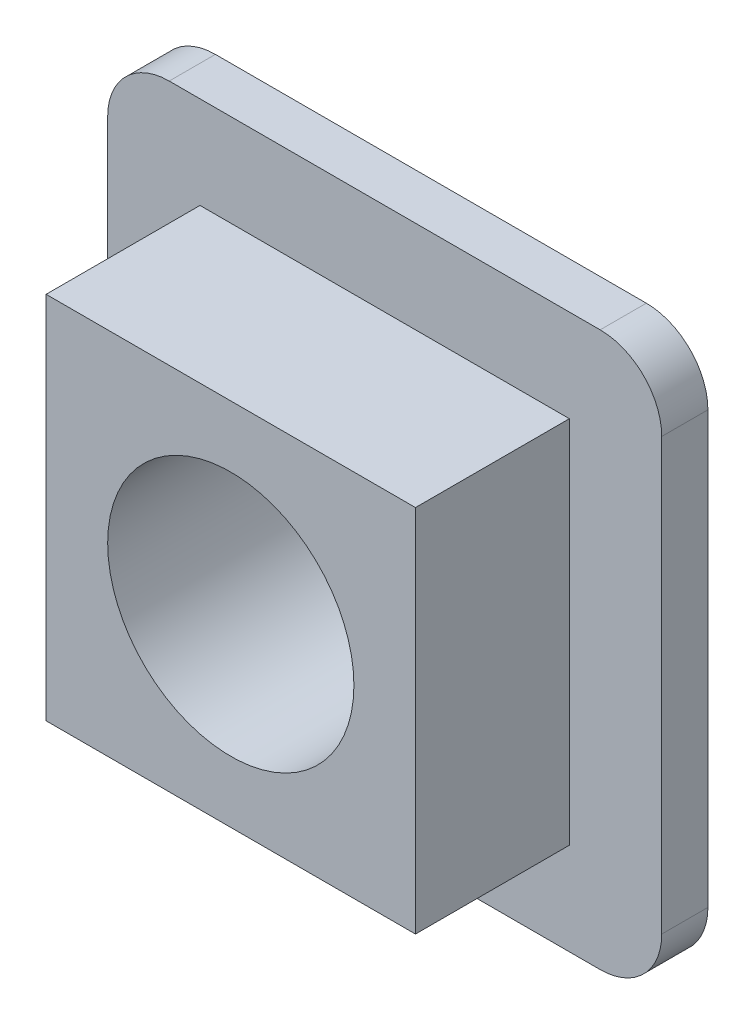
SolidWorks part; units mm, degrees
material "AISI 304"
ref_plane "Front Plane" through (0, 0, 0) normal (0, 0, 1) x (1, 0, 0)
ref_plane "Top Plane" through (0, 0, 0) normal (0, 1, 0) x (1, 0, 0)
ref_plane "Right Plane" through (0, 0, 0) normal (1, 0, 0) x (0, 0, -1)
sketch "Sketch1" plane through (0, 0, 0) normal (0, 0, 1) x (1, 0, 0)
  line L1 (2, 0) -> (16, 0)
  line L2 (0, 2) -> (0, 16)
  line L3 (2, 18) -> (16, 18)
  line L4 (18, 2) -> (18, 16)
  arc A0 (16, 18) -> (18, 16) centre (16, 16) cw
  arc A1 (18, 2) -> (16, 0) centre (16, 2) cw
  arc A2 (2, 0) -> (0, 2) centre (2, 2) cw
  arc A3 (0, 16) -> (2, 18) centre (2, 16) cw
  point P7 (18, 18)
  point P10 (18, 0)
  point P13 (0, 0)
  point P16 (0, 18)
  dimension "D3" = 2
  dimension "D1" = 18
  dimension "D2" = 18
extrude "Boss-Extrude1" add sketch "Sketch1" along normal blind 1.5
sketch "Sketch2" plane through (0, 0, 1.5) normal (0, 0, 1) x (1, 0, 0)
  line L0 (16, 18) -> (2, 18) construction
  line L1 (3, 15) -> (15, 15)
  line L2 (3, 15) -> (3, 3)
  line L3 (3, 3) -> (15, 3)
  line L4 (15, 15) -> (15, 3)
  line L5 (2, 0) -> (16, 0) construction
  line L6 (0, 16) -> (0, 2) construction
  line L7 (18, 2) -> (18, 16) construction
  dimension "D1" = 3
  dimension "D2" = 3
  dimension "D3" = 3
  dimension "D4" = 3
extrude "Boss-Extrude2" add sketch "Sketch2" along normal blind 5
sketch "Sketch3" plane through (0, 0, 6.5) normal (0, 0, 1) x (1, 0, 0)
  circle A0 centre (9, 9) radius 4
extrude "Cut-Extrude1" cut sketch "Sketch3" against normal through all
